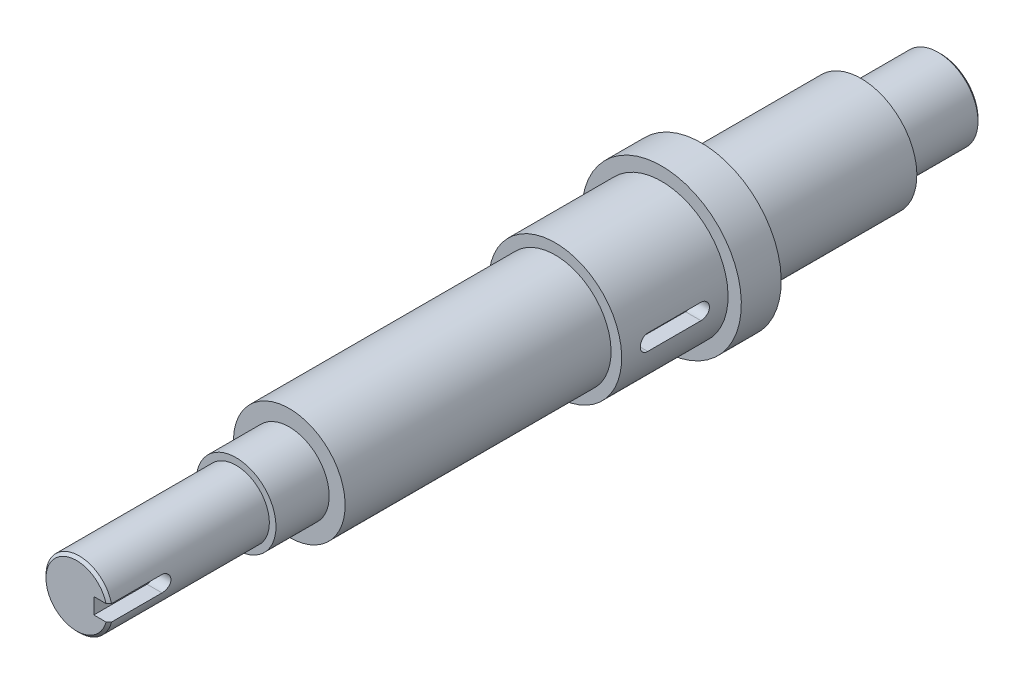
SolidWorks part; units mm, degrees
ref_plane "Front Plane" through (0, 0, 0) normal (0, 0, 1) x (1, 0, 0)
ref_plane "Top Plane" through (0, 0, 0) normal (0, 1, 0) x (1, 0, 0)
ref_plane "Right Plane" through (0, 0, 0) normal (1, 0, 0) x (0, 0, -1)
sketch "Sketch2" plane through (0, 0, 0) normal (1, 0, 0) x (0, 0, -1)
  line L0 (0, 0) -> (-225, 0) construction
  line L1 (-225, 12.5) -> (-225, 0)
  line L2 (-45, 21) -> (-45, 25)
  line L3 (-225, 12.5) -> (-165, 12.5)
  line L4 (-165, 12.5) -> (-165, 15)
  line L5 (-165, 15) -> (-145, 15)
  line L6 (-145, 15) -> (-145, 21)
  line L7 (-145, 21) -> (-45, 21)
  line L8 (-45, 25) -> (-5, 25)
  line L9 (-5, 25) -> (-5, 30)
  line L10 (-5, 30) -> (10, 30)
  line L11 (10, 30) -> (10, 21)
  line L12 (10, 21) -> (70, 21)
  line L13 (70, 21) -> (70, 15)
  line L14 (70, 15) -> (100, 15)
  line L15 (100, 15) -> (100, 0)
  line L16 (100, 0) -> (0, 0) construction
  line L17 (-225, 0) -> (100, 0)
  point P15 (-155, 15)
  point P21 (0, 0)
  dimension "D1" = 25
  dimension "D2" = 30
  dimension "D3" = 42
  dimension "D4" = 325
  dimension "D5" = 50
  dimension "D6" = 60
  dimension "D7" = 100
  dimension "D8" = 15
  dimension "D9" = 30
  dimension "D10" = 60
  dimension "D11" = 40
  dimension "D12" = 60
  dimension "D13" = 100
  dimension "D14" = 20
revolve "Revolve1" add sketch "Sketch2" angle 360 about L17
hole_wizard "M8x1.0 Tapped Hole1" positions "3DSketch1" profile "Sketch3" tap size "M8x1.0" standard "ANSI Metric"
sketch3d "3DSketch1"
  line L0 (0, 0, -100) -> (0, 0, -70) construction
  point P0 (0, 0, -100)
sketch "Sketch3" plane through (0, 0, -100) normal (1, 0, 0) x (0, 1, 0)
  line L0 (0, 0) -> (0, 21.103)
  line L1 (0, 21.103) -> (3.5, 19)
  line L2 (3.5, 19) -> (3.5, 0)
  line L5 (3.5, 0) -> (0, 0)
  line L10 (0, 21.103) -> (-3.5, 19) construction
  line L11 (0, -6.35) -> (0, 107.95) construction
  dimension "Tap Drill Dia." = 7
  dimension "Tap Drill Depth" = 19
  dimension "Drill Angle" = 118
cosmetic thread "Hole Thread1" parameters "D1"=16, "D2"=8
ref_plane "Plane1" through (12.5, 0, 0) normal (1, 0, 0) x (0, 0, -1)
sketch "Sketch4" plane through (12.5, 0, 0) normal (1, 0, 0) x (0, 0, -1)
  line L0 (-225, 0) -> (-205, 0) construction
  line L1 (-225, 12.5) -> (-225, -12.5) construction
  line L2 (-205, 3) -> (-225, 3)
  line L3 (-225, 3) -> (-225, -3)
  line L4 (-205, -3) -> (-225, -3)
  arc A0 (-205, -3) -> (-205, 3) centre (-205, 0) ccw
  dimension "D1" = 6
  dimension "D2" = 20
extrude "Cut-Extrude3" cut sketch "Sketch4" against normal blind 6
ref_plane "Plane2" through (25, 0, 0) normal (1, 0, 0) x (0, 0, -1)
sketch "Sketch5" plane through (25, 0, 0) normal (1, 0, 0) x (0, 0, -1)
  line L0 (-5, 25) -> (-5, -25) construction
  line L1 (-15, 0) -> (-5, 0) construction
  line L2 (-35, 0) -> (-45, 0) construction
  line L3 (-35, 0) -> (-15, 0) construction
  line L4 (-35, 3) -> (-15, 3)
  line L5 (-35, -3) -> (-15, -3)
  line L6 (-45, 21) -> (-45, -21) construction
  arc A0 (-35, 3) -> (-35, -3) centre (-35, 0) ccw
  arc A1 (-15, -3) -> (-15, 3) centre (-15, 0) ccw
  point P4 (-25, 0)
  dimension "D1" = 6
  dimension "D2" = 20
  dimension "D3" = 10
extrude "Cut-Extrude4" cut sketch "Sketch5" against normal blind 6
chamfer "Chamfer1" distance 1 angle 45 2 edges at (-12.5, 0, 225) (0, -15, -100)
fillet "Fillet1" radius 1 1 edges at (0, -15, -70)
